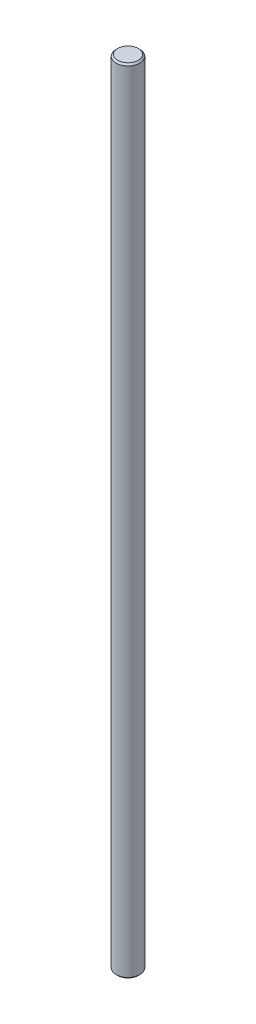
SolidWorks part; units mm, degrees
ref_plane "Front Plane" through (0, 0, 0) normal (0, 0, 1) x (1, 0, 0)
ref_plane "Top Plane" through (0, 0, 0) normal (0, 1, 0) x (1, 0, 0)
ref_plane "Right Plane" through (0, 0, 0) normal (1, 0, 0) x (0, 0, -1)
sketch "Sketch1" plane through (0, 0, 0) normal (0, 1, 0) x (1, 0, 0)
  circle A0 centre (0, 0) radius 1.5
  dimension "D1" = 3
extrude "Boss-Extrude1" add sketch "Sketch1" along normal blind 100
chamfer "Chamfer1" distance 0.2 angle 45 2 edges at (0, 0, 1.5) (0, 100, 1.5)
